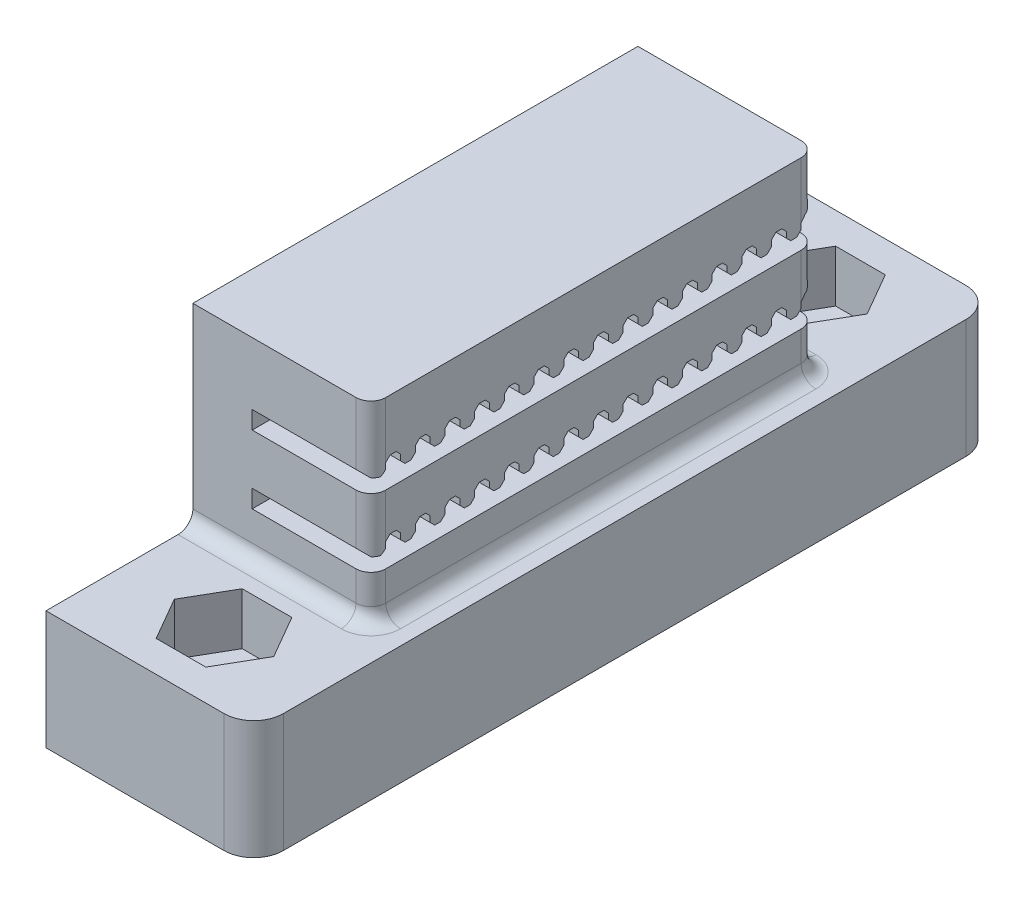
SolidWorks part; units mm, degrees
ref_plane "Alzado" through (0, 0, 0) normal (0, 0, 1) x (1, 0, 0)
ref_plane "Planta" through (0, 0, 0) normal (0, 1, 0) x (1, 0, 0)
ref_plane "Vista lateral" through (0, 0, 0) normal (1, 0, 0) x (0, 0, -1)
sketch "Croquis1" plane through (0, 0, 0) normal (0, 1, 0) x (1, 0, 0)
  line L0 (0, 25) -> (14, 25) construction
  line L1 (0, 0) -> (14, 0)
  line L2 (0, 0) -> (0, 50)
  line L3 (0, 50) -> (14, 50)
  line L4 (14, 0) -> (14, 50)
  line L5 (7, 50) -> (7, 0) construction
  circle A0 centre (7, 45) radius 1.65
  circle A1 centre (7, 5) radius 1.65
  dimension "D3" = 3.3
  dimension "D1" = 50
  dimension "D2" = 14
  dimension "D4" = 20
extrude "Saliente-Extruir1" add sketch "Croquis1" along normal blind 8
sketch "Croquis2" plane through (0, 8, 0) normal (0, 1, 0) x (1, 0, 0)
  line L1 (10.3486, 45) -> (8.6743, 47.9)
  line L2 (8.6743, 47.9) -> (5.3257, 47.9)
  line L3 (5.3257, 47.9) -> (3.6514, 45)
  line L4 (3.6514, 45) -> (5.3257, 42.1)
  line L5 (5.3257, 42.1) -> (8.6743, 42.1)
  line L6 (8.6743, 42.1) -> (10.3486, 45)
  line L7 (10.3486, 5) -> (8.6743, 7.9)
  line L8 (8.6743, 7.9) -> (5.3257, 7.9)
  line L9 (5.3257, 7.9) -> (3.6514, 5)
  line L10 (3.6514, 5) -> (5.3257, 2.1)
  line L11 (5.3257, 2.1) -> (8.6743, 2.1)
  line L12 (8.6743, 2.1) -> (10.3486, 5)
  circle A2 centre (7, 45) radius 2.9 construction
  circle A3 centre (7, 5) radius 2.9 construction
  dimension "D1" = 5.8
  dimension "D2" = 5.8
extrude "Cortar-Extruir1" cut sketch "Croquis2" against normal blind 3.5
sketch "Croquis3" plane through (0, 8, 0) normal (0, 1, 0) x (1, 0, 0)
  line L0 (0, 50) -> (0, 0) construction
  line L1 (0, 39.9) -> (14, 39.9)
  line L2 (0, 39.9) -> (0, 9.9)
  line L3 (0, 9.9) -> (14, 9.9)
  line L4 (14, 39.9) -> (14, 9.9)
  line L5 (14, 0) -> (14, 50) construction
  line L6 (5.3257, 42.1) -> (8.6743, 42.1) construction
  dimension "D1" = 30
  dimension "D2" = 2.2
extrude "Saliente-Extruir3" add sketch "Croquis3" along normal blind 13
sketch "Croquis4" plane through (14, 0, 0) normal (1, 0, 0) x (0, 0, -1)
  line L0 (39.9, 21) -> (39.9, 8) construction
  line L5 (39.9, 8) -> (50, 8) construction
  point P31 (9.9, 12.9)
  line B0 (39.9, 12.9) -> (39.9, 11)
  line B1 (39.9, 11) -> (9.9, 11)
  line B2 (39.4, 12.9) -> (39.2, 12.9)
  line B3 (38.9, 12.6) -> (38.9, 12.2)
  line B4 (38.6, 11.9) -> (38.2, 11.9)
  line B5 (37.9, 12.2) -> (37.9, 12.6)
  line B6 (39.9, 12.9) -> (39.4, 12.9)
  line B7 (37.6, 12.9) -> (37.4, 12.9)
  line B8 (39.2, 12.9) -> (38.9, 12.6)
  line B9 (38.9, 12.2) -> (38.6, 11.9)
  line B10 (38.2, 11.9) -> (37.9, 12.2)
  line B11 (37.9, 12.6) -> (37.6, 12.9)
  line B12 (37.4, 12.9) -> (37.2, 12.9)
  line B13 (36.9, 12.6) -> (36.9, 12.2)
  line B14 (36.6, 11.9) -> (36.2, 11.9)
  line B15 (35.9, 12.2) -> (35.9, 12.6)
  line B16 (35.6, 12.9) -> (35.4, 12.9)
  line B17 (37.2, 12.9) -> (36.9, 12.6)
  line B18 (36.9, 12.2) -> (36.6, 11.9)
  line B19 (36.2, 11.9) -> (35.9, 12.2)
  line B20 (35.9, 12.6) -> (35.6, 12.9)
  line B21 (35.4, 12.9) -> (35.2, 12.9)
  line B22 (34.9, 12.6) -> (34.9, 12.2)
  line B23 (34.6, 11.9) -> (34.2, 11.9)
  line B24 (33.9, 12.2) -> (33.9, 12.6)
  line B25 (33.6, 12.9) -> (33.4, 12.9)
  line B26 (35.2, 12.9) -> (34.9, 12.6)
  line B27 (34.9, 12.2) -> (34.6, 11.9)
  line B28 (34.2, 11.9) -> (33.9, 12.2)
  line B29 (33.9, 12.6) -> (33.6, 12.9)
  line B30 (33.4, 12.9) -> (33.2, 12.9)
  line B31 (32.9, 12.6) -> (32.9, 12.2)
  line B32 (32.6, 11.9) -> (32.2, 11.9)
  line B33 (31.9, 12.2) -> (31.9, 12.6)
  line B34 (31.6, 12.9) -> (31.4, 12.9)
  line B35 (33.2, 12.9) -> (32.9, 12.6)
  line B36 (32.9, 12.2) -> (32.6, 11.9)
  line B37 (32.2, 11.9) -> (31.9, 12.2)
  line B38 (31.9, 12.6) -> (31.6, 12.9)
  line B39 (31.4, 12.9) -> (31.2, 12.9)
  line B40 (30.9, 12.6) -> (30.9, 12.2)
  line B41 (30.6, 11.9) -> (30.2, 11.9)
  line B42 (29.9, 12.2) -> (29.9, 12.6)
  line B43 (29.6, 12.9) -> (29.4, 12.9)
  line B44 (31.2, 12.9) -> (30.9, 12.6)
  line B45 (30.9, 12.2) -> (30.6, 11.9)
  line B46 (30.2, 11.9) -> (29.9, 12.2)
  line B47 (29.9, 12.6) -> (29.6, 12.9)
  line B48 (29.4, 12.9) -> (29.2, 12.9)
  line B49 (28.9, 12.6) -> (28.9, 12.2)
  line B50 (28.6, 11.9) -> (28.2, 11.9)
  line B51 (27.9, 12.2) -> (27.9, 12.6)
  line B52 (27.6, 12.9) -> (27.4, 12.9)
  line B53 (29.2, 12.9) -> (28.9, 12.6)
  line B54 (28.9, 12.2) -> (28.6, 11.9)
  line B55 (28.2, 11.9) -> (27.9, 12.2)
  line B56 (27.9, 12.6) -> (27.6, 12.9)
  line B57 (27.4, 12.9) -> (27.2, 12.9)
  line B58 (26.9, 12.6) -> (26.9, 12.2)
  line B59 (26.6, 11.9) -> (26.2, 11.9)
  line B60 (25.9, 12.2) -> (25.9, 12.6)
  line B61 (25.6, 12.9) -> (25.4, 12.9)
  line B62 (27.2, 12.9) -> (26.9, 12.6)
  line B63 (26.9, 12.2) -> (26.6, 11.9)
  line B64 (26.2, 11.9) -> (25.9, 12.2)
  line B65 (25.9, 12.6) -> (25.6, 12.9)
  line B66 (25.4, 12.9) -> (25.2, 12.9)
  line B67 (24.9, 12.6) -> (24.9, 12.2)
  line B68 (24.6, 11.9) -> (24.2, 11.9)
  line B69 (23.9, 12.2) -> (23.9, 12.6)
  line B70 (23.6, 12.9) -> (23.4, 12.9)
  line B71 (25.2, 12.9) -> (24.9, 12.6)
  line B72 (24.9, 12.2) -> (24.6, 11.9)
  line B73 (24.2, 11.9) -> (23.9, 12.2)
  line B74 (23.9, 12.6) -> (23.6, 12.9)
  line B75 (23.4, 12.9) -> (23.2, 12.9)
  line B76 (22.9, 12.6) -> (22.9, 12.2)
  line B77 (22.6, 11.9) -> (22.2, 11.9)
  line B78 (21.9, 12.2) -> (21.9, 12.6)
  line B79 (21.6, 12.9) -> (21.4, 12.9)
  line B80 (23.2, 12.9) -> (22.9, 12.6)
  line B81 (22.9, 12.2) -> (22.6, 11.9)
  line B82 (22.2, 11.9) -> (21.9, 12.2)
  line B83 (21.9, 12.6) -> (21.6, 12.9)
  line B84 (21.4, 12.9) -> (21.2, 12.9)
  line B85 (20.9, 12.6) -> (20.9, 12.2)
  line B86 (20.6, 11.9) -> (20.2, 11.9)
  line B87 (19.9, 12.2) -> (19.9, 12.6)
  line B88 (19.6, 12.9) -> (19.4, 12.9)
  line B89 (21.2, 12.9) -> (20.9, 12.6)
  line B90 (20.9, 12.2) -> (20.6, 11.9)
  line B91 (20.2, 11.9) -> (19.9, 12.2)
  line B92 (19.9, 12.6) -> (19.6, 12.9)
  line B93 (19.4, 12.9) -> (19.2, 12.9)
  line B94 (18.9, 12.6) -> (18.9, 12.2)
  line B95 (18.6, 11.9) -> (18.2, 11.9)
  line B96 (17.9, 12.2) -> (17.9, 12.6)
  line B97 (17.6, 12.9) -> (17.4, 12.9)
  line B98 (19.2, 12.9) -> (18.9, 12.6)
  line B99 (18.9, 12.2) -> (18.6, 11.9)
  line B100 (18.2, 11.9) -> (17.9, 12.2)
  line B101 (17.9, 12.6) -> (17.6, 12.9)
  line B102 (17.4, 12.9) -> (17.2, 12.9)
  line B103 (16.9, 12.6) -> (16.9, 12.2)
  line B104 (16.6, 11.9) -> (16.2, 11.9)
  line B105 (15.9, 12.2) -> (15.9, 12.6)
  line B106 (15.6, 12.9) -> (15.4, 12.9)
  line B107 (17.2, 12.9) -> (16.9, 12.6)
  line B108 (16.9, 12.2) -> (16.6, 11.9)
  line B109 (16.2, 11.9) -> (15.9, 12.2)
  line B110 (15.9, 12.6) -> (15.6, 12.9)
  line B111 (15.4, 12.9) -> (15.2, 12.9)
  line B112 (14.9, 12.6) -> (14.9, 12.2)
  line B113 (14.6, 11.9) -> (14.2, 11.9)
  line B114 (13.9, 12.2) -> (13.9, 12.6)
  line B115 (13.6, 12.9) -> (13.4, 12.9)
  line B116 (15.2, 12.9) -> (14.9, 12.6)
  line B117 (14.9, 12.2) -> (14.6, 11.9)
  line B118 (14.2, 11.9) -> (13.9, 12.2)
  line B119 (13.9, 12.6) -> (13.6, 12.9)
  line B120 (13.4, 12.9) -> (13.2, 12.9)
  line B121 (12.9, 12.6) -> (12.9, 12.2)
  line B122 (12.6, 11.9) -> (12.2, 11.9)
  line B123 (11.9, 12.2) -> (11.9, 12.6)
  line B124 (11.6, 12.9) -> (11.4, 12.9)
  line B125 (13.2, 12.9) -> (12.9, 12.6)
  line B126 (12.9, 12.2) -> (12.6, 11.9)
  line B127 (12.2, 11.9) -> (11.9, 12.2)
  line B128 (11.9, 12.6) -> (11.6, 12.9)
  line B129 (11.4, 12.9) -> (11.2, 12.9)
  line B130 (10.9, 12.6) -> (10.9, 12.2)
  line B131 (10.6, 11.9) -> (10.2, 11.9)
  line B132 (9.9, 12.2) -> (9.9, 11)
  line B133 (11.2, 12.9) -> (10.9, 12.6)
  line B134 (10.9, 12.2) -> (10.6, 11.9)
  line B135 (10.2, 11.9) -> (9.9, 12.2)
  line B136 (39.9, 17.5) -> (39.9, 15.6)
  line B137 (39.9, 15.6) -> (9.9, 15.6)
  line B138 (39.4, 17.5) -> (39.2, 17.5)
  line B139 (38.9, 17.2) -> (38.9, 16.8)
  line B140 (38.6, 16.5) -> (38.2, 16.5)
  line B141 (37.9, 16.8) -> (37.9, 17.2)
  line B142 (39.9, 17.5) -> (39.4, 17.5)
  line B143 (37.6, 17.5) -> (37.4, 17.5)
  line B144 (39.2, 17.5) -> (38.9, 17.2)
  line B145 (38.9, 16.8) -> (38.6, 16.5)
  line B146 (38.2, 16.5) -> (37.9, 16.8)
  line B147 (37.9, 17.2) -> (37.6, 17.5)
  line B148 (37.4, 17.5) -> (37.2, 17.5)
  line B149 (36.9, 17.2) -> (36.9, 16.8)
  line B150 (36.6, 16.5) -> (36.2, 16.5)
  line B151 (35.9, 16.8) -> (35.9, 17.2)
  line B152 (35.6, 17.5) -> (35.4, 17.5)
  line B153 (37.2, 17.5) -> (36.9, 17.2)
  line B154 (36.9, 16.8) -> (36.6, 16.5)
  line B155 (36.2, 16.5) -> (35.9, 16.8)
  line B156 (35.9, 17.2) -> (35.6, 17.5)
  line B157 (35.4, 17.5) -> (35.2, 17.5)
  line B158 (34.9, 17.2) -> (34.9, 16.8)
  line B159 (34.6, 16.5) -> (34.2, 16.5)
  line B160 (33.9, 16.8) -> (33.9, 17.2)
  line B161 (33.6, 17.5) -> (33.4, 17.5)
  line B162 (35.2, 17.5) -> (34.9, 17.2)
  line B163 (34.9, 16.8) -> (34.6, 16.5)
  line B164 (34.2, 16.5) -> (33.9, 16.8)
  line B165 (33.9, 17.2) -> (33.6, 17.5)
  line B166 (33.4, 17.5) -> (33.2, 17.5)
  line B167 (32.9, 17.2) -> (32.9, 16.8)
  line B168 (32.6, 16.5) -> (32.2, 16.5)
  line B169 (31.9, 16.8) -> (31.9, 17.2)
  line B170 (31.6, 17.5) -> (31.4, 17.5)
  line B171 (33.2, 17.5) -> (32.9, 17.2)
  line B172 (32.9, 16.8) -> (32.6, 16.5)
  line B173 (32.2, 16.5) -> (31.9, 16.8)
  line B174 (31.9, 17.2) -> (31.6, 17.5)
  line B175 (31.4, 17.5) -> (31.2, 17.5)
  line B176 (30.9, 17.2) -> (30.9, 16.8)
  line B177 (30.6, 16.5) -> (30.2, 16.5)
  line B178 (29.9, 16.8) -> (29.9, 17.2)
  line B179 (29.6, 17.5) -> (29.4, 17.5)
  line B180 (31.2, 17.5) -> (30.9, 17.2)
  line B181 (30.9, 16.8) -> (30.6, 16.5)
  line B182 (30.2, 16.5) -> (29.9, 16.8)
  line B183 (29.9, 17.2) -> (29.6, 17.5)
  line B184 (29.4, 17.5) -> (29.2, 17.5)
  line B185 (28.9, 17.2) -> (28.9, 16.8)
  line B186 (28.6, 16.5) -> (28.2, 16.5)
  line B187 (27.9, 16.8) -> (27.9, 17.2)
  line B188 (27.6, 17.5) -> (27.4, 17.5)
  line B189 (29.2, 17.5) -> (28.9, 17.2)
  line B190 (28.9, 16.8) -> (28.6, 16.5)
  line B191 (28.2, 16.5) -> (27.9, 16.8)
  line B192 (27.9, 17.2) -> (27.6, 17.5)
  line B193 (27.4, 17.5) -> (27.2, 17.5)
  line B194 (26.9, 17.2) -> (26.9, 16.8)
  line B195 (26.6, 16.5) -> (26.2, 16.5)
  line B196 (25.9, 16.8) -> (25.9, 17.2)
  line B197 (25.6, 17.5) -> (25.4, 17.5)
  line B198 (27.2, 17.5) -> (26.9, 17.2)
  line B199 (26.9, 16.8) -> (26.6, 16.5)
  line B200 (26.2, 16.5) -> (25.9, 16.8)
  line B201 (25.9, 17.2) -> (25.6, 17.5)
  line B202 (25.4, 17.5) -> (25.2, 17.5)
  line B203 (24.9, 17.2) -> (24.9, 16.8)
  line B204 (24.6, 16.5) -> (24.2, 16.5)
  line B205 (23.9, 16.8) -> (23.9, 17.2)
  line B206 (23.6, 17.5) -> (23.4, 17.5)
  line B207 (25.2, 17.5) -> (24.9, 17.2)
  line B208 (24.9, 16.8) -> (24.6, 16.5)
  line B209 (24.2, 16.5) -> (23.9, 16.8)
  line B210 (23.9, 17.2) -> (23.6, 17.5)
  line B211 (23.4, 17.5) -> (23.2, 17.5)
  line B212 (22.9, 17.2) -> (22.9, 16.8)
  line B213 (22.6, 16.5) -> (22.2, 16.5)
  line B214 (21.9, 16.8) -> (21.9, 17.2)
  line B215 (21.6, 17.5) -> (21.4, 17.5)
  line B216 (23.2, 17.5) -> (22.9, 17.2)
  line B217 (22.9, 16.8) -> (22.6, 16.5)
  line B218 (22.2, 16.5) -> (21.9, 16.8)
  line B219 (21.9, 17.2) -> (21.6, 17.5)
  line B220 (21.4, 17.5) -> (21.2, 17.5)
  line B221 (20.9, 17.2) -> (20.9, 16.8)
  line B222 (20.6, 16.5) -> (20.2, 16.5)
  line B223 (19.9, 16.8) -> (19.9, 17.2)
  line B224 (19.6, 17.5) -> (19.4, 17.5)
  line B225 (21.2, 17.5) -> (20.9, 17.2)
  line B226 (20.9, 16.8) -> (20.6, 16.5)
  line B227 (20.2, 16.5) -> (19.9, 16.8)
  line B228 (19.9, 17.2) -> (19.6, 17.5)
  line B229 (19.4, 17.5) -> (19.2, 17.5)
  line B230 (18.9, 17.2) -> (18.9, 16.8)
  line B231 (18.6, 16.5) -> (18.2, 16.5)
  line B232 (17.9, 16.8) -> (17.9, 17.2)
  line B233 (17.6, 17.5) -> (17.4, 17.5)
  line B234 (19.2, 17.5) -> (18.9, 17.2)
  line B235 (18.9, 16.8) -> (18.6, 16.5)
  line B236 (18.2, 16.5) -> (17.9, 16.8)
  line B237 (17.9, 17.2) -> (17.6, 17.5)
  line B238 (17.4, 17.5) -> (17.2, 17.5)
  line B239 (16.9, 17.2) -> (16.9, 16.8)
  line B240 (16.6, 16.5) -> (16.2, 16.5)
  line B241 (15.9, 16.8) -> (15.9, 17.2)
  line B242 (15.6, 17.5) -> (15.4, 17.5)
  line B243 (17.2, 17.5) -> (16.9, 17.2)
  line B244 (16.9, 16.8) -> (16.6, 16.5)
  line B245 (16.2, 16.5) -> (15.9, 16.8)
  line B246 (15.9, 17.2) -> (15.6, 17.5)
  line B247 (15.4, 17.5) -> (15.2, 17.5)
  line B248 (14.9, 17.2) -> (14.9, 16.8)
  line B249 (14.6, 16.5) -> (14.2, 16.5)
  line B250 (13.9, 16.8) -> (13.9, 17.2)
  line B251 (13.6, 17.5) -> (13.4, 17.5)
  line B252 (15.2, 17.5) -> (14.9, 17.2)
  line B253 (14.9, 16.8) -> (14.6, 16.5)
  line B254 (14.2, 16.5) -> (13.9, 16.8)
  line B255 (13.9, 17.2) -> (13.6, 17.5)
  line B256 (13.4, 17.5) -> (13.2, 17.5)
  line B257 (12.9, 17.2) -> (12.9, 16.8)
  line B258 (12.6, 16.5) -> (12.2, 16.5)
  line B259 (11.9, 16.8) -> (11.9, 17.2)
  line B260 (11.6, 17.5) -> (11.4, 17.5)
  line B261 (13.2, 17.5) -> (12.9, 17.2)
  line B262 (12.9, 16.8) -> (12.6, 16.5)
  line B263 (12.2, 16.5) -> (11.9, 16.8)
  line B264 (11.9, 17.2) -> (11.6, 17.5)
  line B265 (11.4, 17.5) -> (11.2, 17.5)
  line B266 (10.9, 17.2) -> (10.9, 16.8)
  line B267 (10.6, 16.5) -> (10.2, 16.5)
  line B268 (9.9, 16.8) -> (9.9, 15.6)
  line B269 (11.2, 17.5) -> (10.9, 17.2)
  line B270 (10.9, 16.8) -> (10.6, 16.5)
  line B271 (10.2, 16.5) -> (9.9, 16.8)
  line M126 (39.9, 8) -> (39.9, 21)
  line M128 (9.9, 21) -> (9.9, 8)
  dimension "D1" = 7.6
  dimension "D2" = 3
sketch_block_instance "Bloque1-1"
sketch_block "Bloque1" parameters "D1"=1.9, "D2"=0.5, "D3"=0.5, "D4"=1, "D5"=1, "D6"=1, "D7"=0.5
sketch_block_instance "Bloque1-2"
extrude "Cortar-Extruir2" cut sketch "Croquis4" against normal blind 10 contours B131 B135 B1 B6 B2 B8 B3 B9 B4 B10 B5 B11 B7 B12 B17 B13 B18 B14 B19 B15 B20 B16 B21 B26 B22 B27 B23 B28 B24 B29 B25 B30 B35 B31 B36 B32 B37 B33 B38 B34 B39 B44 B40 B45 B41 B46 B42 B47 B43 M128 M126 | B267 B271 B137 B142 B138 B144 B139 B145 B140 B146 B141 B147 B143 B148 B153 B149 B154 B150 B155 B151 B156 B152 B157 B162 B158 B163 B159 B164 B160 B165 B161 B166 B171 B167 B172 B168 B173 B169 B174 B170 B175 B180 B176 B181 B177 B182 B178 B183 B179 M128 M126
sketch "Croquis5" plane through (14, 0, 0) normal (1, 0, 0) x (0, 0, -1)
  line L1 (39.9, 8) -> (9.9, 8)
  line L2 (39.9, 8) -> (39.9, 21)
  line L3 (39.9, 21) -> (9.9, 21)
  line L4 (9.9, 8) -> (9.9, 21)
extrude "Cortar-Extruir3" cut sketch "Croquis5" against normal blind 2
fillet "Redondeo2" radius 2 2 edges at (14, 4, -50) (14, 4, 0)
fillet "Redondeo3" radius 1 6 edges at (12, 19.25, -39.9) (12, 9.5, -39.9) (12, 9.5, -9.9) (12, 18.9, -9.9) (12, 13.9, -9.9) (12, 14.25, -39.9)
fillet "Redondeo4" radius 1 5 edges at (5.5, 8, -9.9) (11.7071, 8, -10.1929) (12, 8, -24.9) (11.7071, 8, -39.6071) (5.5, 8, -39.9)
